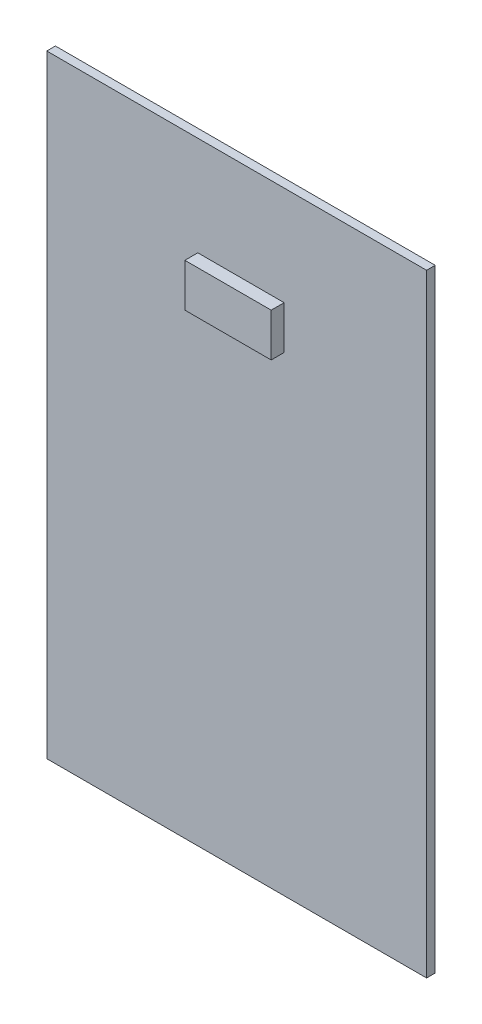
SolidWorks part; units mm, degrees
ref_plane "Front Plane" through (0, 0, 0) normal (0, 0, 1) x (1, 0, 0)
ref_plane "Top Plane" through (0, 0, 0) normal (0, 1, 0) x (1, 0, 0)
ref_plane "Right Plane" through (0, 0, 0) normal (1, 0, 0) x (0, 0, -1)
sketch "Sketch1" plane through (0, 0, 0) normal (0, 0, 1) x (1, 0, 0)
  line L1 (-44, 71) -> (44, 71)
  line L2 (-44, 71) -> (-44, -71)
  line L3 (-44, -71) -> (44, -71)
  line L4 (44, 71) -> (44, -71)
  line L5 (-44, 71) -> (44, -71) construction
  line L6 (-44, -71) -> (44, 71) construction
  point P0 (0, 0)
  dimension "D1" = 142
  dimension "D2" = 88
extrude "Boss-Extrude1" add sketch "Sketch1" along normal blind 2
sketch "Sketch2" plane through (0, 0, 2) normal (0, 0, 1) x (1, 0, 0)
  line L1 (-9.0047, 48) -> (10.9953, 48)
  line L2 (-9.0047, 48) -> (-9.0047, 38)
  line L3 (-9.0047, 38) -> (10.9953, 38)
  line L4 (10.9953, 48) -> (10.9953, 38)
  line L5 (-9.0047, 48) -> (10.9953, 38) construction
  line L6 (-9.0047, 38) -> (10.9953, 48) construction
  line L7 (44, 71) -> (-44, 71) construction
  point P0 (0.9953, 43)
  point P7 (0.9953, 56.877)
  dimension "D1" = 28
  dimension "D2" = 20
  dimension "15" = 10
extrude "Boss-Extrude2" add sketch "Sketch2" along normal blind 3
